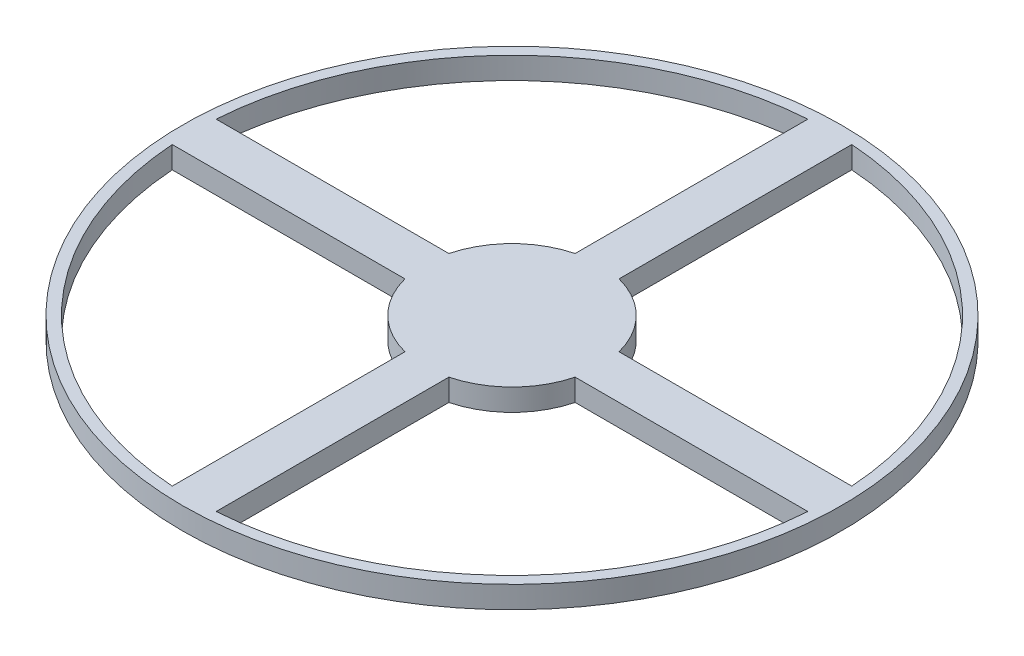
SolidWorks part; units mm, degrees
material "6061-T6 (SS)"
ref_plane "Front Plane" through (0, 0, 0) normal (0, 0, 1) x (1, 0, 0)
ref_plane "Top Plane" through (0, 0, 0) normal (0, 1, 0) x (1, 0, 0)
ref_plane "Right Plane" through (0, 0, 0) normal (1, 0, 0) x (0, 0, -1)
sketch "Center" plane through (0, 0, 0) normal (0, 1, 0) x (1, 0, 0)
  circle A0 centre (0, 0) radius 25.4
  dimension "D" = 50.8
sketch "Ring" plane through (0, 0, 0) normal (0, 1, 0) x (1, 0, 0)
  circle A0 centre (0, 0) radius 95.25
  circle A1 centre (0, 0) radius 92.075
  dimension "D1" = 190.5
  dimension "D2" = 3.175
sketch "Beams" plane through (0, 0, 0) normal (0, 1, 0) x (1, 0, 0)
  line L0 (-91.8558, 6.35) -> (-24.5934, 6.35)
  line L1 (-91.8558, -6.35) -> (-24.5934, -6.35)
  circle A0 centre (0, 0) radius 92.075 construction
  circle A8 centre (0, 0) radius 25.4 construction
  arc A12 (-24.5934, -6.35) -> (-24.5934, 6.35) centre (0, 0) cw
  circle A13 centre (0, 0) radius 92.075 construction
  arc A14 (-91.8558, 6.35) -> (-91.8558, -6.35) centre (0, 0) ccw
  point P25 (0, 0)
  dimension "D3" = 50.8
  dimension "D4" = 184.15
  dimension "D1" = 6.35
  dimension "D2" = 12.7
extrude "Beam" add sketch "Beams" along normal blind 6.35
sketch "axis" plane through (0, 0, 0) normal (0, 0, 1) x (1, 0, 0)
  line L0 (0, 0) -> (0, 68.0201) construction
extrude "Center1" add sketch "Center" along normal blind 6.35
extrude "Ring1" add sketch "Ring" along normal blind 6.35
pattern_circular "CirPattern3" count 4 over 360 about axis through (0, 0, 0) along (0, 1, 0) of "Beam"
sketch "Sketch8" plane through (0, 0, 0) normal (0, 1, 0) x (1, 0, 0)
  circle A0 centre (0, 0) radius 9.525
equation "\"H\"= .25"
equation "\"D1@Center1\"=\"H\""
equation "\"D1@Beam\"=\"H\""
equation "\"D1@Ring1\"=\"H\""
equation "\"D\"= 2"
equation "\"a\"= .125"
equation "\"T\"= .125"
equation "\"N\"= 4"
equation "\"D1@CirPattern3\"=\"N\""
